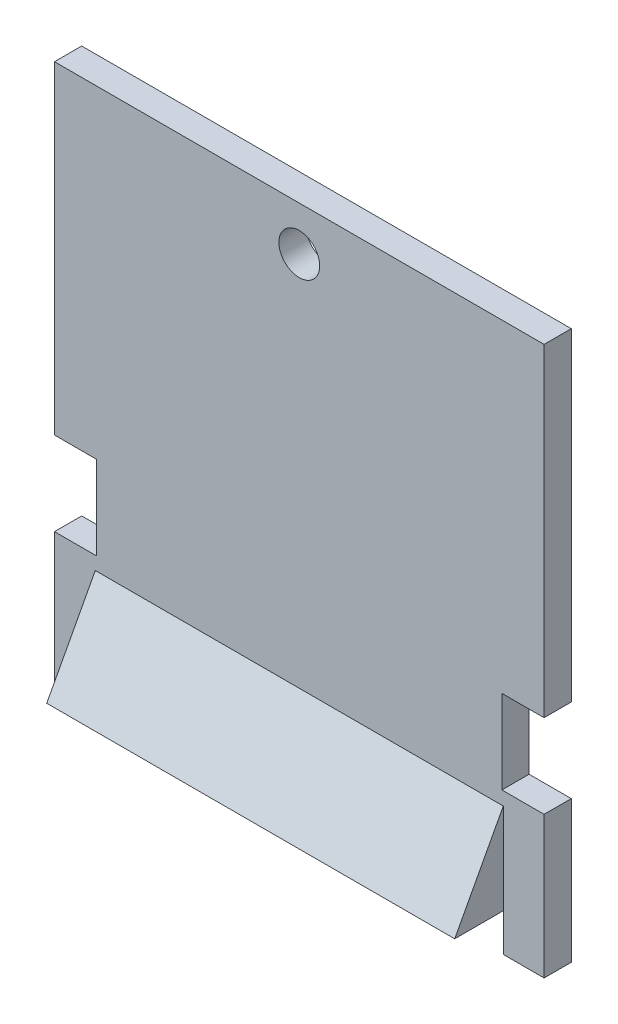
SolidWorks part; units mm, degrees
ref_plane "Front Plane" through (0, 0, 0) normal (0, 0, 1) x (1, 0, 0)
ref_plane "Top Plane" through (0, 0, 0) normal (0, 1, 0) x (1, 0, 0)
ref_plane "Right Plane" through (0, 0, 0) normal (1, 0, 0) x (0, 0, -1)
sketch "Sketch1" plane through (0, 0, 0) normal (1, 0, 0) x (0, 0, -1)
  line L0 (0, 0) -> (0, 40.35)
  line L1 (0, 40.35) -> (-2, 40.35)
  line L2 (-2, 40.35) -> (-2, 9.45)
  line L3 (-2, 9.45) -> (-5.57, 2.78)
  line L4 (-5.57, 2.78) -> (-2, 2.78)
  line L5 (-2, 2.78) -> (-2, 0)
  line L6 (-2, 0) -> (0, 0)
  dimension "D1" = 2
  dimension "D2" = 6.67
  dimension "D3" = 2.78
  dimension "D4" = 3.57
  dimension "D5" = 30.9
extrude "Boss-Extrude1" add sketch "Sketch1" along normal mid plane 36
sketch "Sketch2" plane through (0, 0, 0) normal (0, 0, -1) x (-1, 0, 0)
  line L0 (-18, 0) -> (18, 0) construction
  line L1 (-15, 0) -> (15, 0)
  line L2 (-15, 0) -> (-15, 2.78)
  line L3 (-15, 2.78) -> (15, 2.78)
  line L4 (15, 0) -> (15, 2.78)
  line L5 (-18, 2.78) -> (18, 2.78) construction
  line L6 (-18, 40.35) -> (18, 40.35) construction
  circle A0 centre (0, 37.1) radius 1.5
  point P6 (0, 2.78)
  dimension "D2" = 3
  dimension "D1" = 30
  dimension "D3" = 3.25
extrude "Cut-Extrude1" cut sketch "Sketch2" against normal through all
sketch "Sketch3" plane through (0, 0, 0) normal (0, 0, -1) x (-1, 0, 0)
  line L0 (-18, 0) -> (-18, 40.35) construction
  line L1 (-18, 16.575) -> (-14.9, 16.575)
  line L2 (-18, 16.575) -> (-18, 10.425)
  line L3 (-18, 10.425) -> (-14.9, 10.425)
  line L4 (-14.9, 16.575) -> (-14.9, 10.425)
  line L5 (18, 0) -> (18, 40.35) construction
  line L6 (18, 16.575) -> (14.9, 16.575)
  line L7 (18, 16.575) -> (18, 10.425)
  line L8 (18, 10.425) -> (14.9, 10.425)
  line L9 (14.9, 16.575) -> (14.9, 10.425)
  line L11 (-18, 0) -> (-15, 0) construction
  point P12 (-18, 13.5)
  dimension "D1" = 3.1
  dimension "D2" = 6.15
  dimension "D3" = 13.5
extrude "Cut-Extrude2" cut sketch "Sketch3" against normal through all
sketch "Sketch4" plane through (0, 0, 2) normal (0, 0, 1) x (1, 0, 0)
  line L0 (18, 2.78) -> (-18, 2.78) construction
  line L1 (-18, 10.425) -> (-15, 10.425)
  line L2 (-18, 10.425) -> (-18, 2.78)
  line L3 (-18, 2.78) -> (-15, 2.78)
  line L4 (-15, 10.425) -> (-15, 2.78)
  line L6 (18, 10.425) -> (15, 10.425)
  line L7 (18, 10.425) -> (18, 2.78)
  line L8 (18, 2.78) -> (15, 2.78)
  line L9 (15, 10.425) -> (15, 2.78)
  dimension "D1" = 30
extrude "Cut-Extrude3" cut sketch "Sketch4" along normal through all
